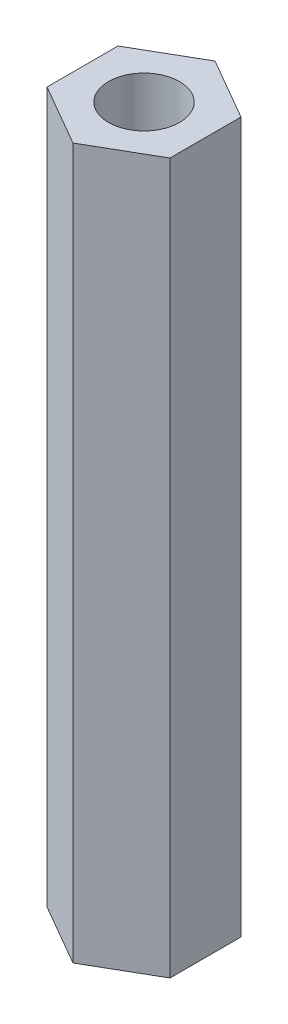
SolidWorks part; units mm, degrees
ref_plane "Face" through (0, 0, 0) normal (0, 0, 1) x (1, 0, 0)
ref_plane "Dessus" through (0, 0, 0) normal (0, 1, 0) x (1, 0, 0)
ref_plane "Droite" through (0, 0, 0) normal (1, 0, 0) x (0, 0, -1)
sketch "Esquisse1" plane through (0, 0, 0) normal (0, 1, 0) x (1, 0, 0)
  line L0 (0, 0) -> (0, 5.5688) construction
  line L1 (0, 5) -> (-4.3301, 2.5)
  line L2 (-4.3301, 2.5) -> (-4.3301, -2.5)
  line L3 (-4.3301, -2.5) -> (0, -5)
  line L4 (0, -5) -> (4.3301, -2.5)
  line L5 (4.3301, -2.5) -> (4.3301, 2.5)
  line L6 (4.3301, 2.5) -> (0, 5)
  circle A0 centre (0, 0) radius 4.3301 construction
  circle A1 centre (0, 0) radius 2.5
  dimension "D1" = 10
  dimension "D2" = 5
extrude "Extrusion1" add sketch "Esquisse1" along normal blind 50
